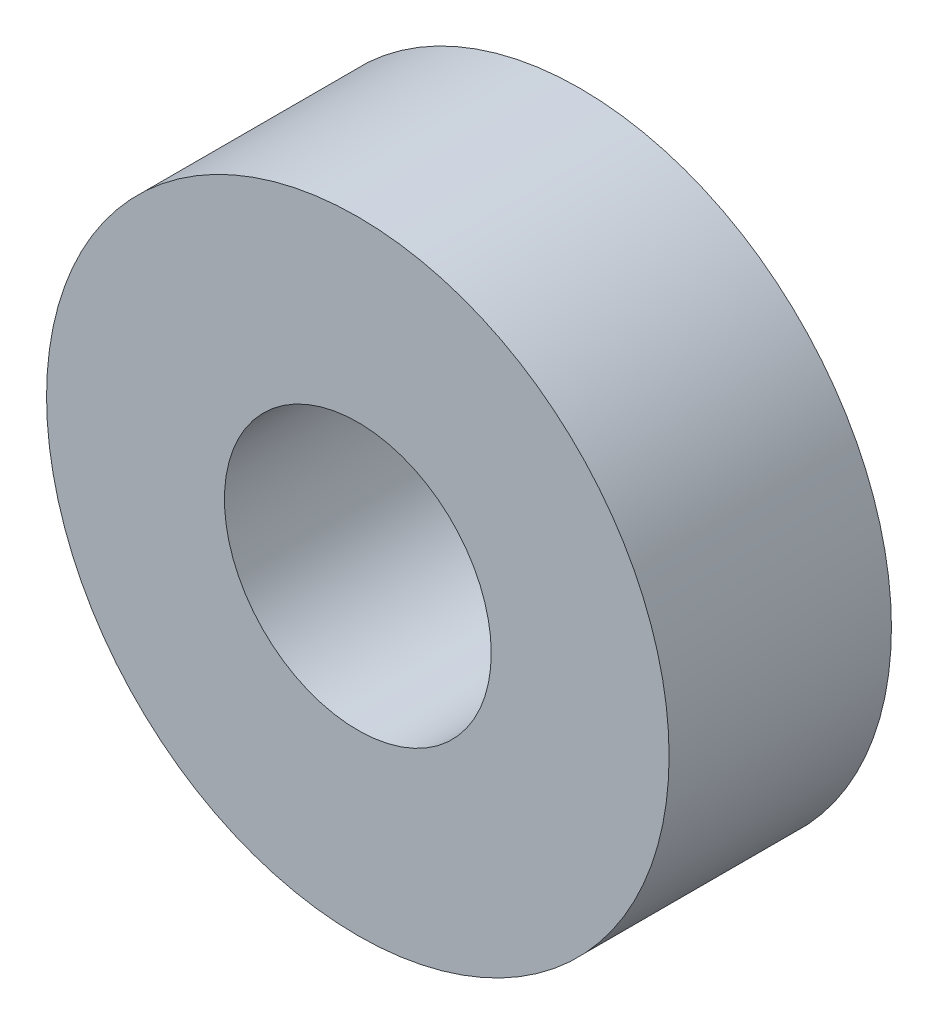
SolidWorks part; units mm, degrees
ref_plane "Front Plane" through (0, 0, 0) normal (0, 0, 1) x (1, 0, 0)
ref_plane "Top Plane" through (0, 0, 0) normal (0, 1, 0) x (1, 0, 0)
ref_plane "Right Plane" through (0, 0, 0) normal (1, 0, 0) x (0, 0, -1)
sketch "Sketch1" plane through (0, 0, 0) normal (0, 0, 1) x (1, 0, 0)
  circle A0 centre (0, 0) radius 7
  circle A1 centre (0, 0) radius 3
  dimension "D1" = 14
  dimension "D2" = 6
extrude "Boss-Extrude1" add sketch "Sketch1" along normal mid plane 5
